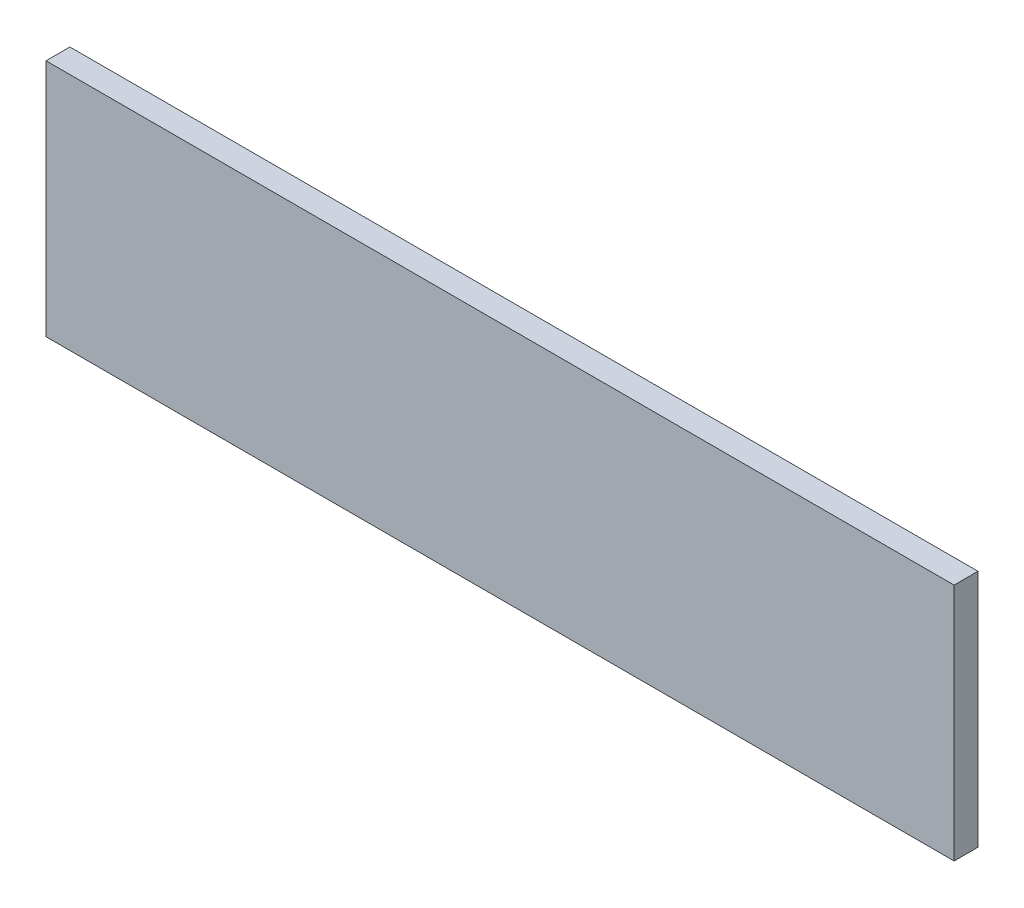
SolidWorks part; units mm, degrees
ref_plane "Front Plane" through (0, 0, 0) normal (0, 0, 1) x (1, 0, 0)
ref_plane "Top Plane" through (0, 0, 0) normal (0, 1, 0) x (1, 0, 0)
ref_plane "Right Plane" through (0, 0, 0) normal (1, 0, 0) x (0, 0, -1)
sketch "Sketch1" plane through (0, 0, 0) normal (0, 0, 1) x (1, 0, 0)
  line L1 (-241.3, -63.5) -> (241.3, -63.5)
  line L2 (-241.3, -63.5) -> (-241.3, 63.5)
  line L3 (-241.3, 63.5) -> (241.3, 63.5)
  line L4 (241.3, -63.5) -> (241.3, 63.5)
  line L5 (-241.3, -63.5) -> (241.3, 63.5) construction
  line L6 (-241.3, 63.5) -> (241.3, -63.5) construction
  point P0 (0, 0)
  dimension "D1" = 482.6
  dimension "D2" = 127
extrude "Boss-Extrude1" add sketch "Sketch1" along normal blind 12.7
